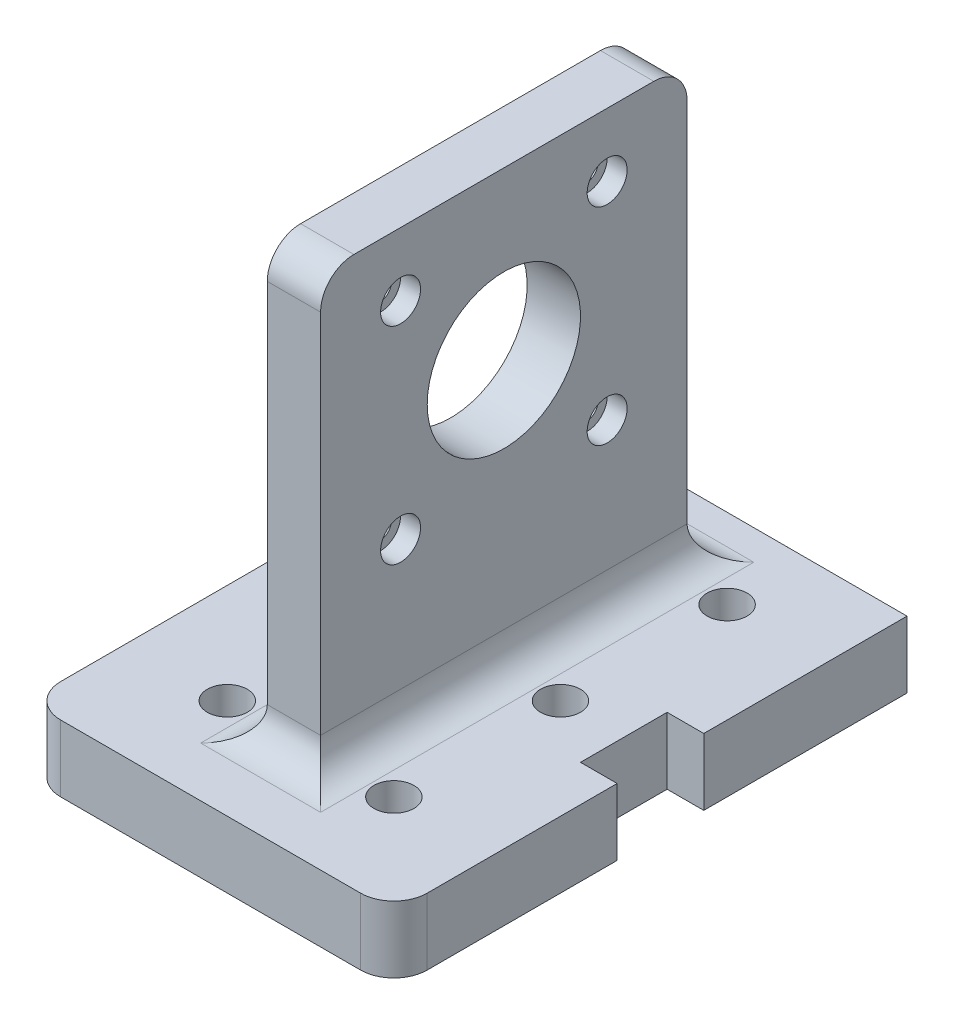
SolidWorks part; units mm, degrees
ref_plane "Front Plane" through (0, 0, 0) normal (0, 0, 1) x (1, 0, 0)
ref_plane "Top Plane" through (0, 0, 0) normal (0, 1, 0) x (1, 0, 0)
ref_plane "Right Plane" through (0, 0, 0) normal (1, 0, 0) x (0, 0, -1)
sketch "Sketch1" plane through (0, 0, 0) normal (0, 1, 0) x (1, 0, 0)
  line L1 (-27.5, 40) -> (27.5, 40)
  line L2 (-27.5, 40) -> (-27.5, -40)
  line L3 (-27.5, -40) -> (27.5, -40)
  line L4 (27.5, 40) -> (27.5, -40)
  line L5 (-27.5, 40) -> (27.5, -40) construction
  line L6 (-27.5, -40) -> (27.5, 40) construction
  point P0 (0, 0)
  dimension "D1" = 55
  dimension "D2" = 80
extrude "Boss-Extrude1" add sketch "Sketch1" along normal blind 10
sketch "Sketch6" plane through (0, 10, 0) normal (0, 1, 0) x (1, 0, 0)
  line L0 (-27.5, -40) -> (27.5, -40) construction
  circle A0 centre (-12.5, -25) radius 1.65
  dimension "D3" = 3.3
  dimension "D1" = 12.5
  dimension "D2" = 15
extrude "Cut-Extrude2" cut sketch "Sketch6" against normal blind 55
pattern_linear "LPattern1" count 3 spacing 25 along (0, 0, -1) of "Cut-Extrude2"
mirror "Mirror3" about plane through (0, 0, 0) normal (1, 0, 0) of "LPattern1", "Cut-Extrude2"
sketch "Sketch8" plane through (0, 10, 0) normal (0, 1, 0) x (1, 0, 0)
  line L1 (-4, 27.5) -> (4, 27.5)
  line L2 (-4, 27.5) -> (-4, -27.5)
  line L3 (-4, -27.5) -> (4, -27.5)
  line L4 (4, 27.5) -> (4, -27.5)
  line L5 (-4, 27.5) -> (4, -27.5) construction
  line L6 (-4, -27.5) -> (4, 27.5) construction
  point P0 (0, 0)
  dimension "D1" = 55
  dimension "D2" = 8
extrude "Boss-Extrude3" add sketch "Sketch8" along normal blind 65
fillet "Fillet3" radius 5 8 edges at (27.5, 5, 40) (-27.5, 5, 40) (0, 75, -27.5) (0, 75, 27.5) (4, 10, 0) (-4, 10, 0) (0, 10, -27.5) (0, 10, 27.5)
sketch "Sketch9" plane through (-4, 0, 0) normal (-1, 0, 0) x (0, 0, 1)
  line L0 (-22.5, 75) -> (22.5, 75) construction
  line L1 (-15.5, 65.5) -> (15.5, 65.5) construction
  line L2 (-15.5, 65.5) -> (-15.5, 34.5) construction
  line L3 (-15.5, 34.5) -> (15.5, 34.5) construction
  line L4 (15.5, 65.5) -> (15.5, 34.5) construction
  line L5 (-15.5, 65.5) -> (15.5, 34.5) construction
  line L6 (-15.5, 34.5) -> (15.5, 65.5) construction
  circle A0 centre (-15.5, 65.5) radius 1.6
  circle A1 centre (15.5, 65.5) radius 1.6
  circle A2 centre (-15.5, 34.5) radius 1.6
  circle A3 centre (15.5, 34.5) radius 1.6
  circle A4 centre (0, 50) radius 11.5
  point P0 (0, 50)
  dimension "D5" = 3.2
  dimension "D6" = 3.2
  dimension "D7" = 3.2
  dimension "D8" = 3.2
  dimension "D9" = 23
  dimension "D1" = 25
  dimension "D2" = 31
  dimension "D3" = 31
  dimension "D4" = 0
extrude "Cut-Extrude3" cut sketch "Sketch9" against normal through all
sketch "Sketch10" plane through (4, 0, 0) normal (1, 0, 0) x (0, 0, -1)
  circle A0 centre (-15.5, 65.5) radius 3
  circle A1 centre (15.5, 65.5) radius 3
  circle A2 centre (15.5, 34.5) radius 3
  circle A3 centre (-15.5, 34.5) radius 3
  dimension "D1" = 6
  dimension "D2" = 6
  dimension "D3" = 6
  dimension "D4" = 6
extrude "Cut-Extrude4" cut sketch "Sketch10" against normal blind 3
sketch "Sketch11" plane through (0, 10, 0) normal (0, 1, 0) x (1, 0, 0)
  circle A0 centre (-12.5, -25) radius 3
  dimension "D1" = 6
extrude "Cut-Extrude5" cut sketch "Sketch11" against normal blind 5 and the other way through all
pattern_linear "LPattern2" count 3 spacing 25 along (0, 0, -1) of "Cut-Extrude5"
mirror "Mirror4" about plane through (0, 0, 0) normal (1, 0, 0) of "LPattern2", "Cut-Extrude5"
sketch "Sketch12" plane through (0, 10, 0) normal (0, 1, 0) x (1, 0, 0)
  line L5 (0, 0) -> (71.7356, 0) construction
  line L6 (27.5, -35) -> (27.5, 40) construction
  line L7 (22, 6.5) -> (33, 6.5)
  line L8 (22, 6.5) -> (22, -6.5)
  line L9 (22, -6.5) -> (33, -6.5)
  line L10 (33, 6.5) -> (33, -6.5)
  line L11 (22, 6.5) -> (33, -6.5) construction
  line L12 (22, -6.5) -> (33, 6.5) construction
  point P2 (27.5, 0)
  dimension "D1" = 11
  dimension "D2" = 13
extrude "Cut-Extrude6" cut sketch "Sketch12" against normal through all
sketch "Sketch13" plane through (0, 10, 0) normal (0, 1, 0) x (1, 0, 0)
  line L0 (-12.5, 25) -> (-12.5, 37) construction
  line L1 (-12.5, 37) -> (34.8598, 37)
  line L2 (34.8598, 37) -> (34.8598, 45.8535)
  line L3 (34.8598, 45.8535) -> (-44.4821, 45.8535)
  line L4 (-44.4821, 45.8535) -> (-44.4821, 37)
  line L5 (-44.4821, 37) -> (-12.5, 37)
  dimension "D1" = 12
extrude "Cut-Extrude7" cut sketch "Sketch13" against normal blind 10
